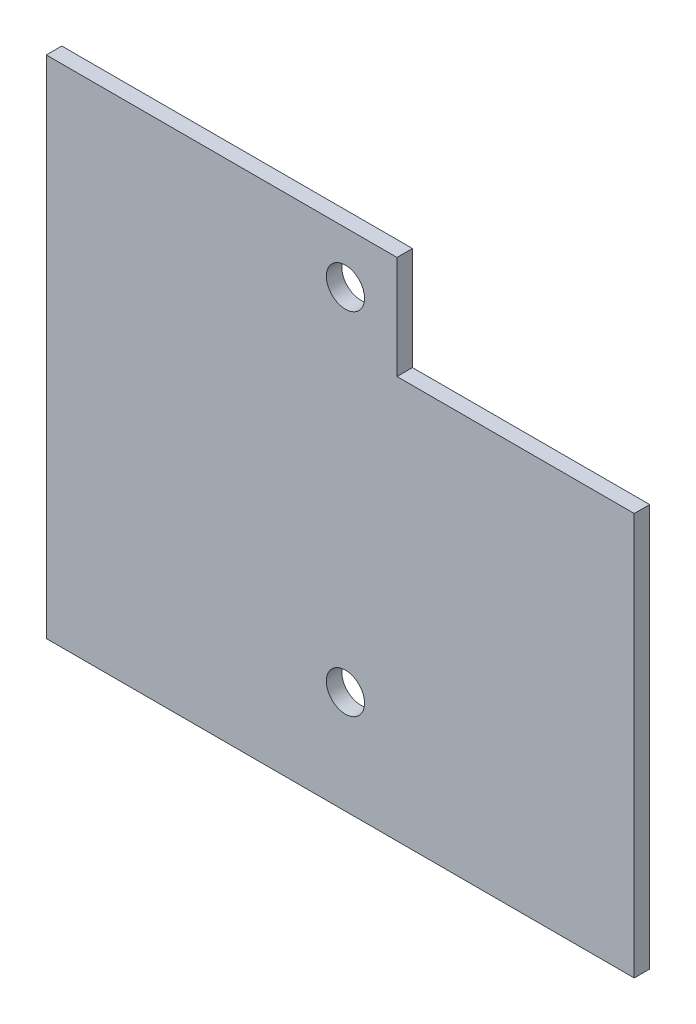
SolidWorks part; units mm, degrees
material "Thornel Mat VMA"
ref_plane "Front" through (0, 0, 0) normal (0, 0, 1) x (1, 0, 0)
ref_plane "Top" through (0, 0, 0) normal (0, 1, 0) x (1, 0, 0)
ref_plane "Right" through (0, 0, 0) normal (1, 0, 0) x (0, 0, -1)
sketch "Эскиз1" plane through (0, 0, 0) normal (0, 0, 1) x (1, 0, 0)
  line L0 (0, 0) -> (0, 49)
  line L1 (0, 49) -> (34, 49)
  line L2 (34, 49) -> (34, 39)
  line L3 (34, 39) -> (57, 39)
  line L4 (57, 39) -> (57, 0)
  line L5 (57, 0) -> (0, 0)
  circle A0 centre (29, 44) radius 1.85
  circle A1 centre (29, 10) radius 1.85
  dimension "D4" = 3.7
  dimension "D5" = 34
  dimension "D6" = 5
  dimension "D7" = 29
  dimension "D1" = 57
  dimension "D2" = 49
  dimension "D3" = 23
  dimension "D8" = 39
extrude "Вытянуть1" add sketch "Эскиз1" along normal blind 1.5
